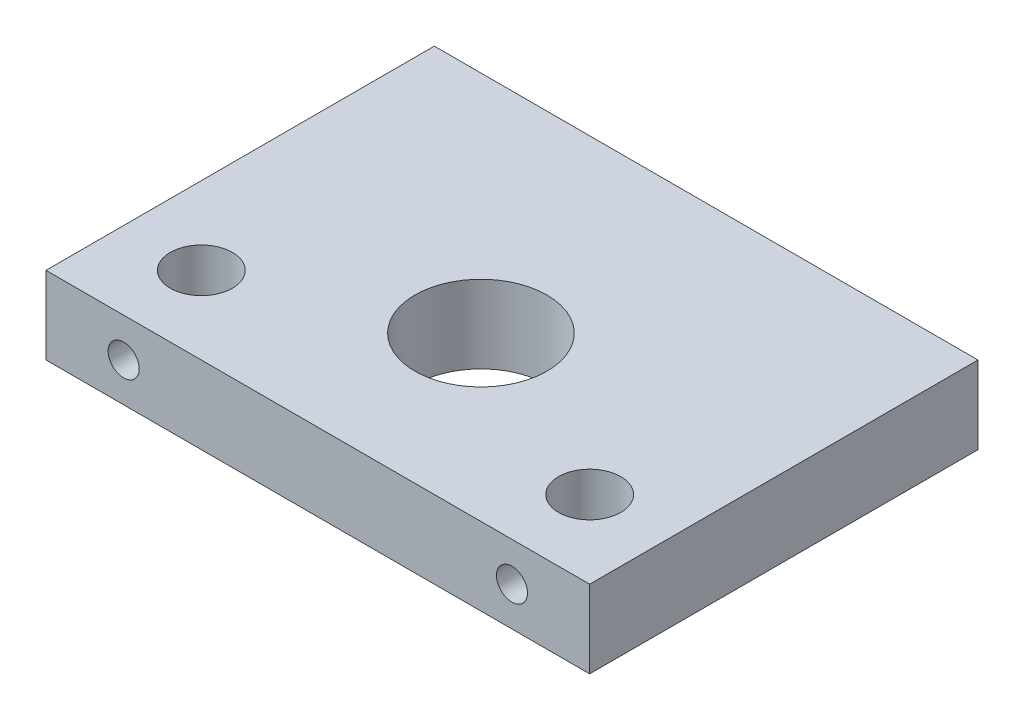
SolidWorks part; units mm, degrees
ref_plane "Front Plane" through (0, 0, 0) normal (0, 0, 1) x (1, 0, 0)
ref_plane "Top Plane" through (0, 0, 0) normal (0, 1, 0) x (1, 0, 0)
ref_plane "Right Plane" through (0, 0, 0) normal (1, 0, 0) x (0, 0, -1)
sketch "Sketch2" plane through (0, 0, 0) normal (0, 1, 0) x (1, 0, 0)
  line L1 (35, -25) -> (-35, -25)
  line L2 (35, -25) -> (35, 25)
  line L3 (35, 25) -> (-35, 25)
  line L4 (-35, -25) -> (-35, 25)
  line L5 (35, -25) -> (-35, 25) construction
  line L6 (35, 25) -> (-35, -25) construction
  point P0 (0, 0)
  dimension "D1" = 50
  dimension "D2" = 70
extrude "Boss-Extrude1" add sketch "Sketch2" along normal blind 10
sketch "Sketch3" plane through (0, 0, 0) normal (0, -1, 0) x (1, 0, 0)
  line L0 (0, 25) -> (0, -35) construction
  line L1 (-35, 25) -> (35, 25) construction
  line L2 (-35, -25) -> (-35, 25) construction
  circle A0 centre (-25, 15) radius 4
  circle A1 centre (25, 15) radius 4
  dimension "D1" = 8
  dimension "D2" = 10
  dimension "D3" = 10
  dimension "D4" = 50
extrude "Cut-Extrude1" cut sketch "Sketch3" against normal through all
sketch "Sketch4" plane through (0, 0, 25) normal (0, 0, 1) x (1, 0, 0)
  line L0 (35, 5) -> (0, 5) construction
  line L1 (35, 10) -> (35, 0) construction
  line L2 (0, 5) -> (0, 10) construction
  line L3 (-35, 10) -> (35, 10) construction
  circle A0 centre (25, 5) radius 2
  circle A1 centre (-25, 5) radius 2
  dimension "D1" = 4
  dimension "D2" = 10
extrude "Cut-Extrude2" cut sketch "Sketch4" against normal blind 10
sketch "Sketch5" plane through (0, 0, 0) normal (0, -1, 0) x (1, 0, 0)
  circle A0 centre (0, 4) radius 10 construction
  circle A1 centre (0, 4) radius 10
  circle A2 centre (0, 4) radius 8.5
  dimension "D1" = 17
extrude "Cut-Extrude3" cut sketch "Sketch5" against normal through all contours A2
